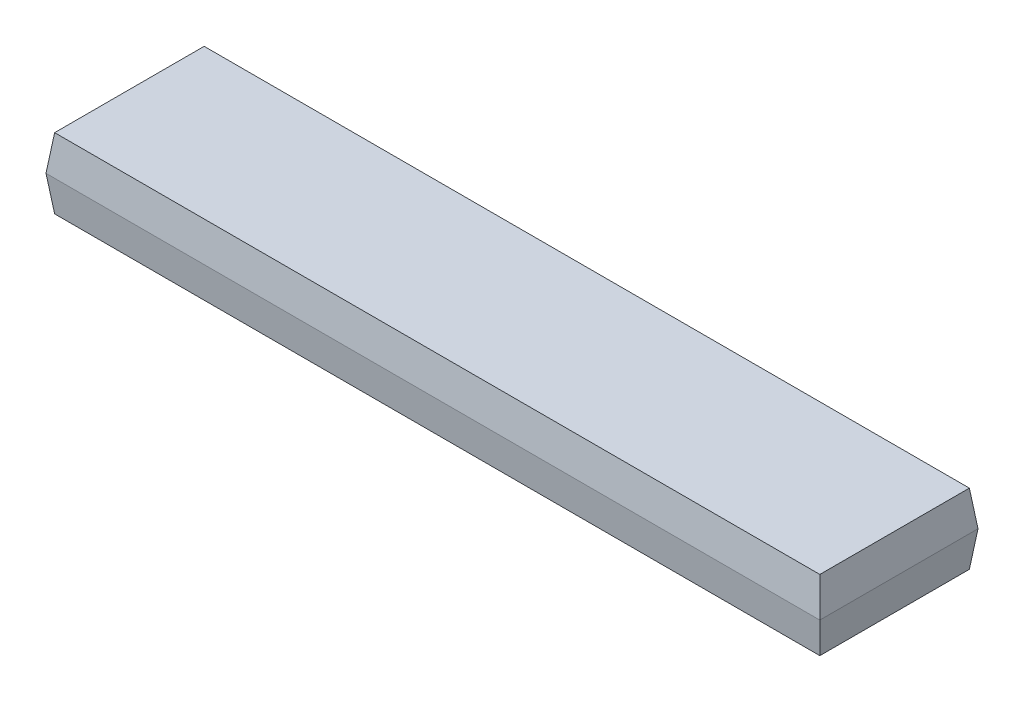
SolidWorks part; units mm, degrees
ref_plane "Plan de face" through (0, 0, 0) normal (0, 0, 1) x (1, 0, 0)
ref_plane "Plan de dessus" through (0, 0, 0) normal (0, 1, 0) x (1, 0, 0)
ref_plane "Plan de droite" through (0, 0, 0) normal (1, 0, 0) x (0, 0, -1)
sketch "Esquisse1" plane through (0, 0, 0) normal (0, 1, 0) x (1, 0, 0)
  line L1 (0, 0) -> (34.8, 0)
  line L2 (0, 0) -> (0, 6.8)
  line L3 (0, 6.8) -> (34.8, 6.8)
  line L4 (34.8, 0) -> (34.8, 6.8)
  dimension "D1" = 6.8
  dimension "D2" = 34.8
extrude "Boss.-Extru.1" add sketch "Esquisse1" along normal blind 1.6 draft 7 draft outward yes
sketch "Esquisse2" plane through (0, 1.6, 0) normal (0, 1, 0) x (1, 0, 0)
  line L0 (-0.1965, -0.1965) -> (34.9965, -0.1965) construction
  line L1 (-0.1965, 6.9965) -> (34.9965, 6.9965)
  line L2 (-0.1965, 6.9965) -> (-0.1965, -0.1965)
  line L3 (-0.1965, -0.1965) -> (34.9965, -0.1965)
  line L4 (34.9965, 6.9965) -> (34.9965, -0.1965)
  line L5 (34.9965, -0.1965) -> (34.9965, 6.9965) construction
extrude "Boss.-Extru.2" add sketch "Esquisse2" along normal blind 1.6 draft 7
